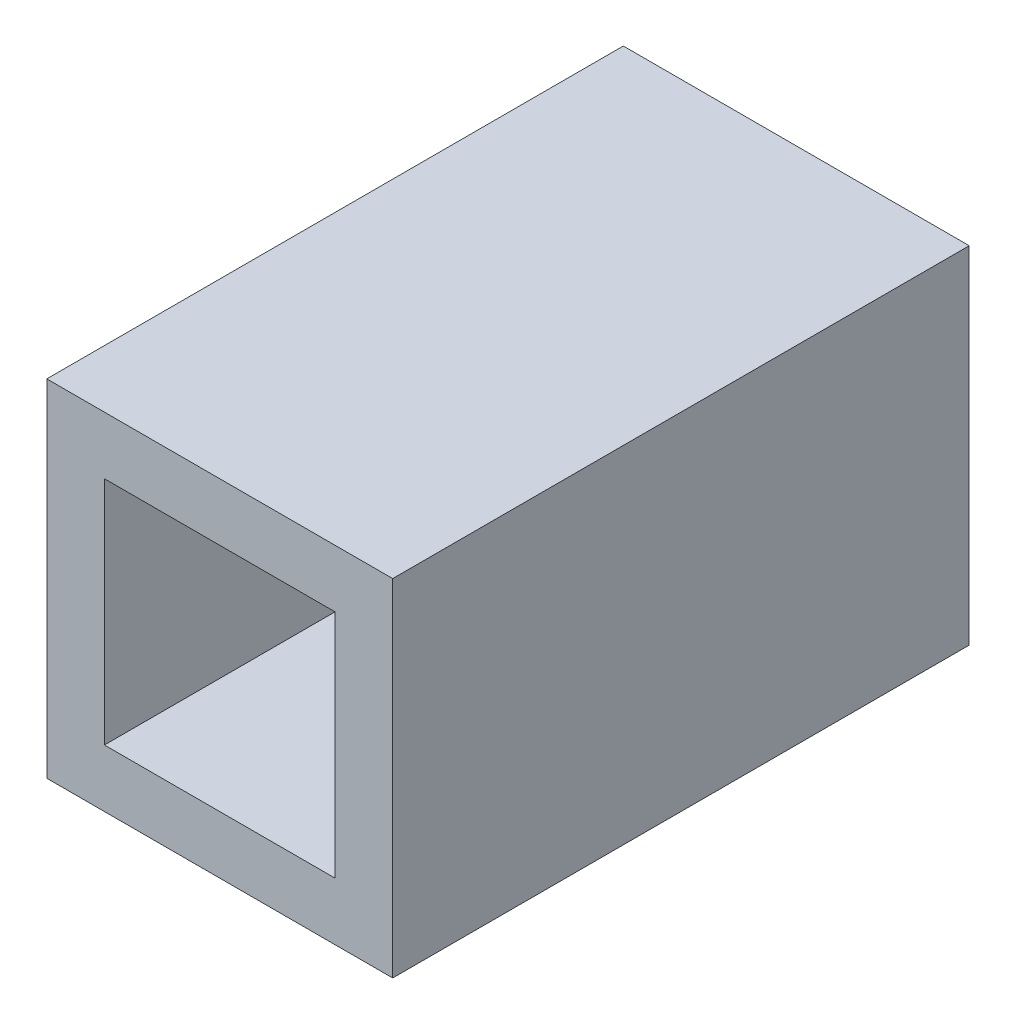
SolidWorks part; units mm, degrees
material "ABS"
ref_plane "Front Plane" through (0, 0, 0) normal (0, 0, 1) x (1, 0, 0)
ref_plane "Top Plane" through (0, 0, 0) normal (0, 1, 0) x (1, 0, 0)
ref_plane "Right Plane" through (0, 0, 0) normal (1, 0, 0) x (0, 0, -1)
sketch "Sketch1" plane through (0, 0, 0) normal (0, 0, 1) x (1, 0, 0)
  line L1 (0, 0) -> (4, 0)
  line L2 (0, 0) -> (0, 4)
  line L3 (0, 4) -> (4, 4)
  line L4 (4, 0) -> (4, 4)
  line L5 (5, 5) -> (-1, 5)
  line L6 (5, 5) -> (5, -1)
  line L7 (5, -1) -> (-1, -1)
  line L8 (-1, 5) -> (-1, -1)
  point P9 (2, 4)
  point P10 (2, 5)
  point P11 (4, 2)
  point P12 (5, 2)
  dimension "D1" = 6
  dimension "D2" = 6
  dimension "D3" = 4
  dimension "D4" = 4
extrude "Boss-Extrude1" add sketch "Sketch1" along normal blind 10
